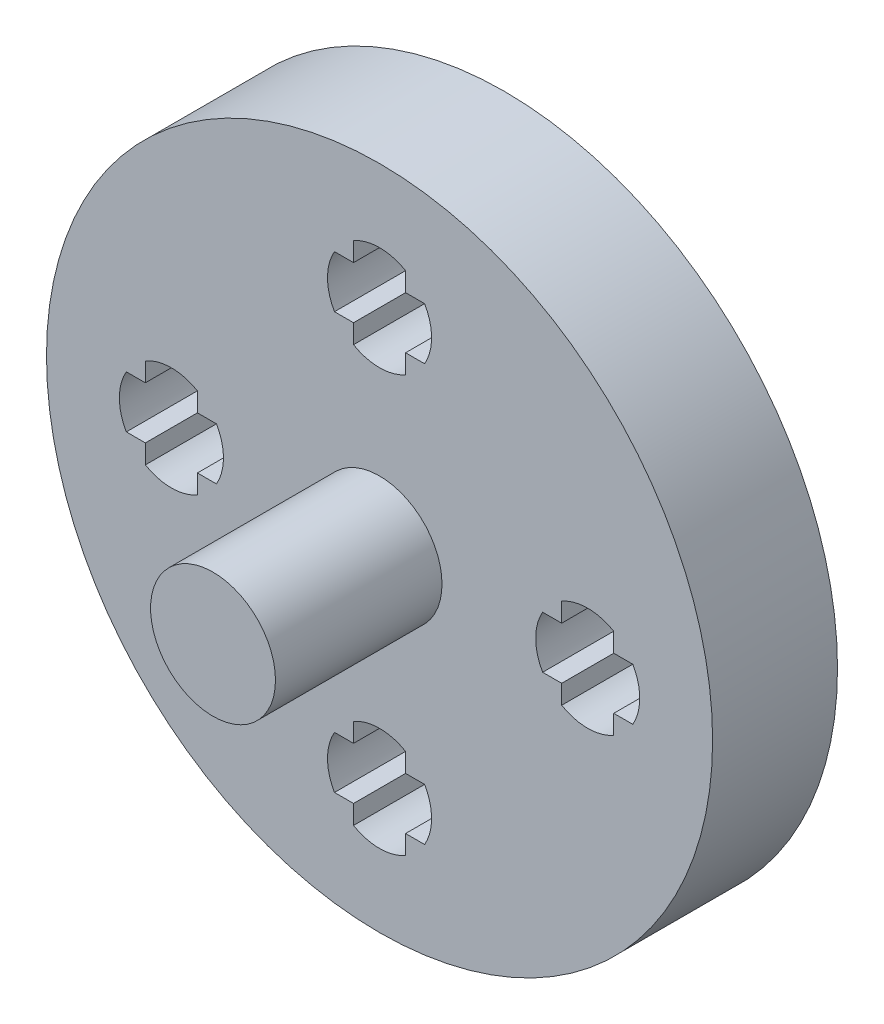
SolidWorks part; units mm, degrees
material "PLA"
ref_plane "Alzado" through (0, 0, 0) normal (0, 0, 1) x (1, 0, 0)
ref_plane "Planta" through (0, 0, 0) normal (0, 1, 0) x (1, 0, 0)
ref_plane "Vista lateral" through (0, 0, 0) normal (1, 0, 0) x (0, 0, -1)
sketch "Croquis1" plane through (0, 0, 0) normal (0, 0, 1) x (1, 0, 0)
  line L0 (0, 12.5) -> (0, 10) construction
  line L1 (0, 10) -> (2.5, 10) construction
  line L2 (0, 11.25) -> (2.1651, 11.25) construction
  line L3 (1.25, 10) -> (1.25, 12.1651) construction
  line L4 (2.1651, 11.25) -> (1.25, 11.25)
  line L5 (1.25, 11.25) -> (1.25, 12.1651)
  line L6 (1.25, 8.75) -> (2.1651, 8.75)
  line L7 (1.25, 7.8349) -> (1.25, 8.75)
  line L8 (-1.25, 8.75) -> (-1.25, 7.8349)
  line L9 (-2.1651, 8.75) -> (-1.25, 8.75)
  line L10 (-1.25, 11.25) -> (-2.1651, 11.25)
  line L11 (-1.25, 12.1651) -> (-1.25, 11.25)
  line L12 (11.25, -1.25) -> (12.1651, -1.25)
  line L13 (11.25, -2.1651) -> (11.25, -1.25)
  line L14 (8.75, -1.25) -> (8.75, -2.1651)
  line L15 (7.8349, -1.25) -> (8.75, -1.25)
  line L16 (8.75, 1.25) -> (7.8349, 1.25)
  line L17 (8.75, 2.1651) -> (8.75, 1.25)
  line L18 (11.25, 1.25) -> (11.25, 2.1651)
  line L19 (12.1651, 1.25) -> (11.25, 1.25)
  line L20 (-1.25, -11.25) -> (-1.25, -12.1651)
  line L21 (-2.1651, -11.25) -> (-1.25, -11.25)
  line L22 (-1.25, -8.75) -> (-2.1651, -8.75)
  line L23 (-1.25, -7.8349) -> (-1.25, -8.75)
  line L24 (1.25, -8.75) -> (1.25, -7.8349)
  line L25 (2.1651, -8.75) -> (1.25, -8.75)
  line L26 (1.25, -11.25) -> (2.1651, -11.25)
  line L27 (1.25, -12.1651) -> (1.25, -11.25)
  line L28 (-11.25, 1.25) -> (-12.1651, 1.25)
  line L29 (-11.25, 2.1651) -> (-11.25, 1.25)
  line L30 (-8.75, 1.25) -> (-8.75, 2.1651)
  line L31 (-7.8349, 1.25) -> (-8.75, 1.25)
  line L32 (-8.75, -1.25) -> (-7.8349, -1.25)
  line L33 (-8.75, -2.1651) -> (-8.75, -1.25)
  line L34 (-11.25, -1.25) -> (-11.25, -2.1651)
  line L35 (-12.1651, -1.25) -> (-11.25, -1.25)
  circle A0 centre (0, 0) radius 16
  circle A1 centre (0, 0) radius 10 construction
  circle A2 centre (0, 10) radius 2.5 construction
  arc A3 (0, 12.5) -> (1.25, 12.1651) centre (0, 10) cw
  arc A4 (2.1651, 11.25) -> (2.5, 10) centre (0, 10) cw
  arc A5 (2.5, 10) -> (2.1651, 8.75) centre (0, 10) cw
  arc A6 (1.25, 7.8349) -> (0, 7.5) centre (0, 10) cw
  arc A7 (0, 7.5) -> (-1.25, 7.8349) centre (0, 10) cw
  arc A8 (-2.1651, 8.75) -> (-2.5, 10) centre (0, 10) cw
  arc A9 (-2.5, 10) -> (-2.1651, 11.25) centre (0, 10) cw
  arc A10 (-1.25, 12.1651) -> (0, 12.5) centre (0, 10) cw
  arc A11 (12.1651, 1.25) -> (12.5, 0) centre (10, 0) cw
  arc A12 (12.5, 0) -> (12.1651, -1.25) centre (10, 0) cw
  arc A13 (11.25, -2.1651) -> (10, -2.5) centre (10, 0) cw
  arc A14 (10, -2.5) -> (8.75, -2.1651) centre (10, 0) cw
  arc A15 (7.8349, -1.25) -> (7.5, 0) centre (10, 0) cw
  arc A16 (7.5, 0) -> (7.8349, 1.25) centre (10, 0) cw
  arc A17 (8.75, 2.1651) -> (10, 2.5) centre (10, 0) cw
  arc A18 (10, 2.5) -> (11.25, 2.1651) centre (10, 0) cw
  arc A19 (1.25, -12.1651) -> (0, -12.5) centre (0, -10) cw
  arc A20 (0, -12.5) -> (-1.25, -12.1651) centre (0, -10) cw
  arc A21 (-2.1651, -11.25) -> (-2.5, -10) centre (0, -10) cw
  arc A22 (-2.5, -10) -> (-2.1651, -8.75) centre (0, -10) cw
  arc A23 (-1.25, -7.8349) -> (0, -7.5) centre (0, -10) cw
  arc A24 (0, -7.5) -> (1.25, -7.8349) centre (0, -10) cw
  arc A25 (2.1651, -8.75) -> (2.5, -10) centre (0, -10) cw
  arc A26 (2.5, -10) -> (2.1651, -11.25) centre (0, -10) cw
  arc A27 (-12.1651, -1.25) -> (-12.5, 0) centre (-10, 0) cw
  arc A28 (-12.5, 0) -> (-12.1651, 1.25) centre (-10, 0) cw
  arc A29 (-11.25, 2.1651) -> (-10, 2.5) centre (-10, 0) cw
  arc A30 (-10, 2.5) -> (-8.75, 2.1651) centre (-10, 0) cw
  arc A31 (-7.8349, 1.25) -> (-7.5, 0) centre (-10, 0) cw
  arc A32 (-7.5, 0) -> (-7.8349, -1.25) centre (-10, 0) cw
  arc A33 (-8.75, -2.1651) -> (-10, -2.5) centre (-10, 0) cw
  arc A34 (-10, -2.5) -> (-11.25, -2.1651) centre (-10, 0) cw
  point P33 (0, 10)
  point P92 (0, 0)
  dimension "D1" = 4
  dimension "D2" = 4
extrude "Saliente-Extruir1" add sketch "Croquis1" along normal blind 6 contours A0 L11 A10 A3 L5 L4 A4 A5 L6 L7 A6 A7 L8 L9 A8 A9 L10 A17 A18 L18 L19 A11 A12 L12 L13 A13 A14 L14 L15 A15 A16 L16 L17 A25 A26 L26 L27 A19 A20 L20 L21 A21 A22 L22 L23 A23 A24 L24
sketch "Croquis2" plane through (0, 0, 6) normal (0, 0, 1) x (1, 0, 0)
  circle A0 centre (0, 0) radius 3
extrude "Saliente-Extruir2" add sketch "Croquis2" along normal blind 8
